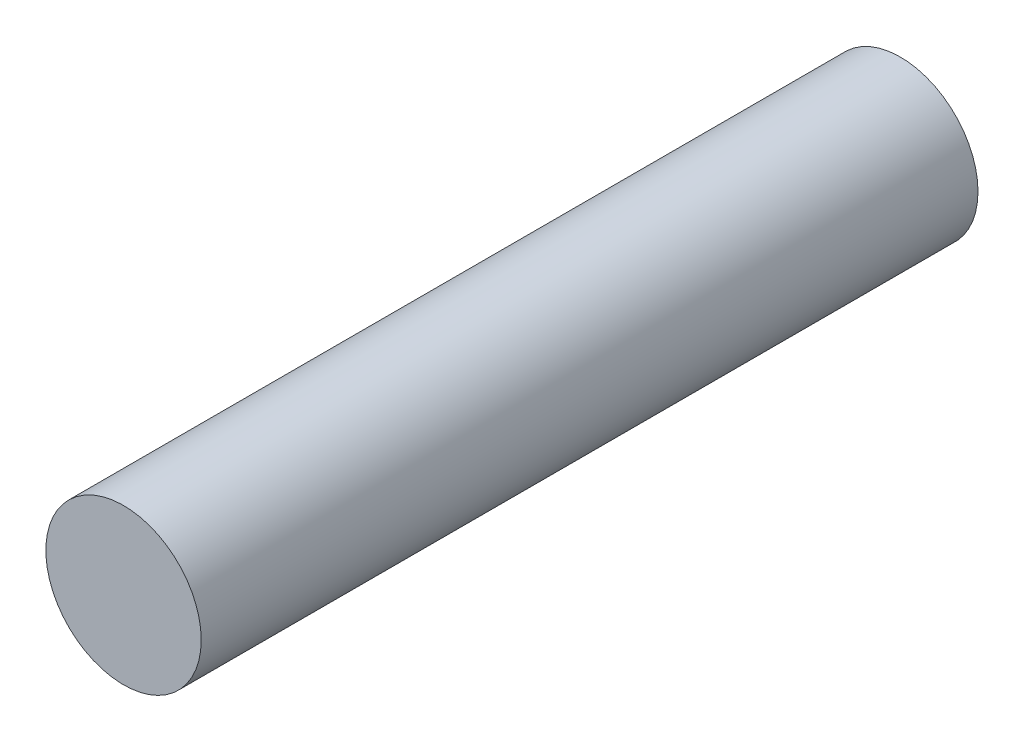
SolidWorks part; units mm, degrees
ref_plane "Front Plane" through (0, 0, 0) normal (0, 0, 1) x (1, 0, 0)
ref_plane "Top Plane" through (0, 0, 0) normal (0, 1, 0) x (1, 0, 0)
ref_plane "Right Plane" through (0, 0, 0) normal (1, 0, 0) x (0, 0, -1)
sketch "Sketch1" plane through (0, 0, 0) normal (0, 0, 1) x (1, 0, 0)
  circle A0 centre (0, 0) radius 1.27
  dimension "D1" = 2.54
extrude "Boss-Extrude1" add sketch "Sketch1" along normal blind 12.7
